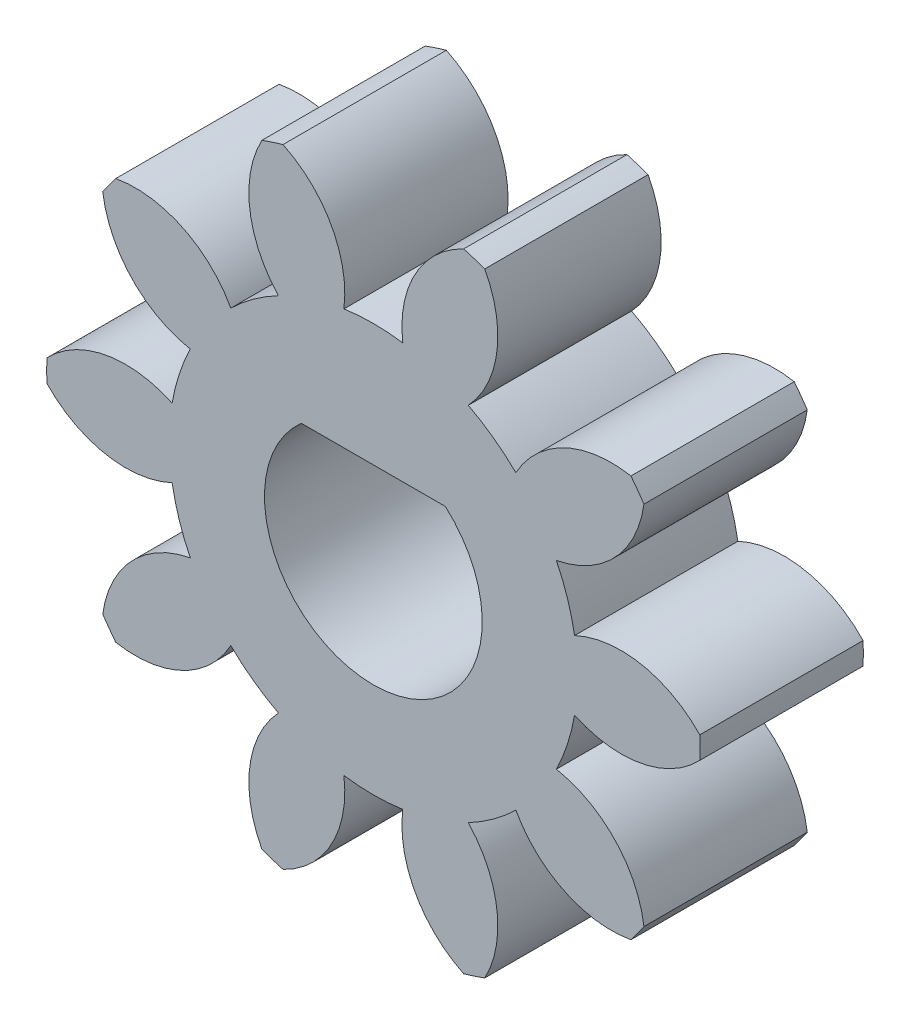
SolidWorks part; units mm, degrees
ref_plane "Front Plane" through (0, 0, 0) normal (0, 0, 1) x (1, 0, 0)
ref_plane "Top Plane" through (0, 0, 0) normal (0, 1, 0) x (1, 0, 0)
ref_plane "Right Plane" through (0, 0, 0) normal (1, 0, 0) x (0, 0, -1)
sketch "Sketch1" plane through (0, 0, 0) normal (0, 0, 1) x (1, 0, 0)
  circle A0 centre (0, 0) radius 6
extrude "Boss-Extrude1" add sketch "Sketch1" along normal blind 3
sketch "Sketch2" plane through (0, 0, 0) normal (0, 0, -1) x (-1, 0, 0)
  line L0 (0, 0) -> (0, 33.0966) construction
  line L1 (0, 0) -> (-7.8154, 24.0534) construction
  line L2 (-0.7789, 4.939) -> (-1.5259, 4.6963) construction
  arc A0 (1.6595, 5.7659) -> (-1.6595, 5.7659) centre (0, 0) ccw construction
  circle A1 centre (0, 0) radius 4.6985 construction
  circle A2 centre (0, 0) radius 3.75 construction
  arc A3 (-1.6595, 5.7659) -> (-0.5404, 3.7109) centre (-2.5245, 3.9627) cw
  arc A5 (1.6595, 5.7659) -> (0.5404, 3.7109) centre (2.5245, 3.9627) ccw
  arc A6 (-1.6595, 5.7659) -> (1.6595, 5.7659) centre (0, 0) cw
  arc A7 (-0.5404, 3.7109) -> (0.5404, 3.7109) centre (0, 0) cw
  circle A8 centre (0, 0) radius 6 construction
  circle A9 centre (0, 0) radius 5 construction
  dimension "D5" = 18
extrude "Cut-Extrude2" cut sketch "Sketch2" against normal through all contours A3 A7 A5 L0
pattern_circular "CirPattern1" count 10 over 360 about axis through (0, 0, 0) along (0, 0, 1) of "Cut-Extrude2"
sketch "Sketch3" [suppressed] plane through (0, 0, 3) normal (0, 0, 1) x (1, 0, 0)
  line L0 (0, 11.1538) -> (0, 0) construction
  line L2 (0, 2.28) -> (7.9946, 16.1272)
  line L4 (-7.9946, 16.1272) -> (0, 2.28)
  line L8 (-5.345, 15.5907) -> (-20.7149, 15.5907) [skipped]
  circle A0 centre (0, 11.1538) radius 4.4369 construction
  arc A1 (-7.9946, 16.1272) -> (7.9946, 16.1272) centre (0, 0) cw
  dimension "D1" = 18
  dimension "D4" = 8.8738
  dimension "D2" = 15.9893
extrude "Cut-Extrude3" [suppressed] cut sketch "Sketch3" against normal blind 10
fillet "Fillet3" [suppressed] radius 2
fillet "Fillet4" [suppressed] radius 2
pattern_circular "CirPattern3" [suppressed] count 6 over 360
sketch "Sketch4" plane through (0, 0, 0) normal (0, 0, -1) x (-1, 0, 0)
  line L0 (0, 0) -> (0, 1.5) construction
  line L1 (-1.3229, 1.5) -> (1.3229, 1.5)
  arc A0 (1.3229, 1.5) -> (-1.3229, 1.5) centre (0, 0) cw
  point P6 (0, 1.5)
  dimension "D2" = 4
  dimension "D1" = 1.5
extrude "Cut-Extrude4" cut sketch "Sketch4" against normal through all
equation "\"module\" = 1.0mm"
equation "\"teeth\"= 10mm"
equation "\"pressureAngle\"= 20deg"
equation "\"gearThickness\"= 3mm"
equation "\"addendumFactor\"= 1mm"
equation "\"dedendumFactor\"= 1.25mm"
equation "\"pitch\"= 1 / ( \"module\" )"
equation "\"addendum\"= \"addendumFactor\" / \"pitch\""
equation "\"dedendum\"= \"dedendumFactor\" / \"pitch\""
equation "\"pitchDiameter\"= \"teeth\" / \"pitch\""
equation "\"D1@Sketch1\" = \"pitchDiameter\" + 2 * \"addendum\""
equation "\"D1@Boss-Extrude1\"=\"gearThickness\""
equation "\"D1@Sketch2\"=\"pitchDiameter\" - 2 * \"dedendum\""
equation "\"D2@Sketch2\"=\"pitchDiameter\" * cos ( \"pressureAngle\" )"
equation "\"D4@Sketch2\"=\"pitchDiameter\"/5"
equation "\"D5@Sketch2\"=180/\"teeth\""
equation "\"D1@CirPattern1\"=\"teeth\""
equation "\"D3@Sketch2\"=\"pitchDiameter\""
equation "\"D6@Sketch2\"=PI/2/\"pitch\"/2"
